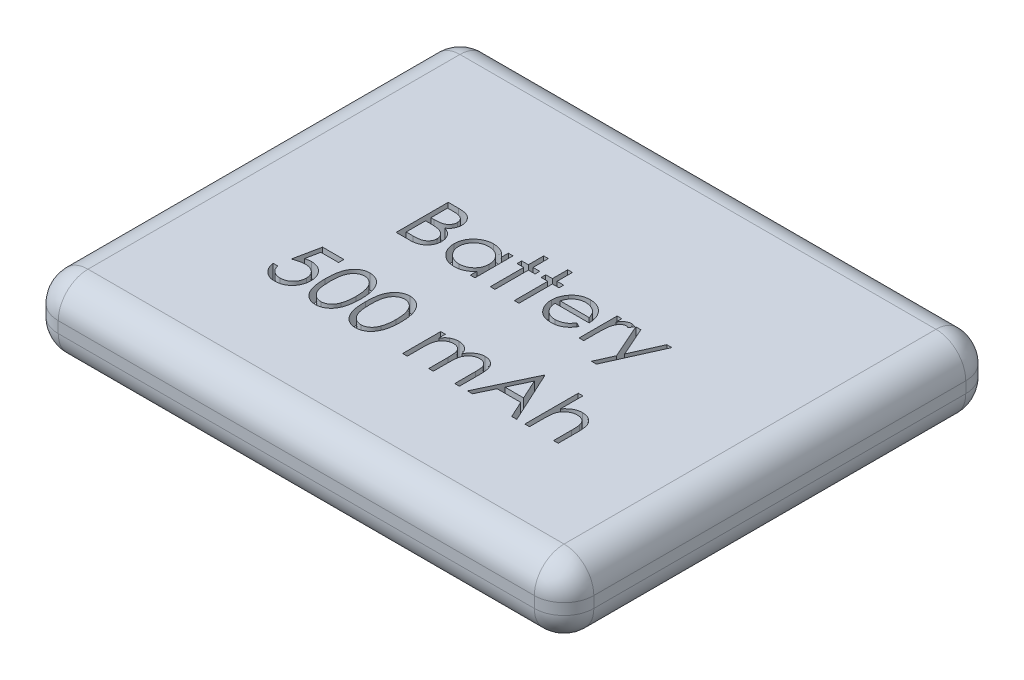
SolidWorks part; units mm, degrees
ref_plane "Front Plane" through (0, 0, 0) normal (0, 0, 1) x (1, 0, 0)
ref_plane "Top Plane" through (0, 0, 0) normal (0, 1, 0) x (1, 0, 0)
ref_plane "Right Plane" through (0, 0, 0) normal (1, 0, 0) x (0, 0, -1)
sketch "Sketch1" plane through (0, 0, 0) normal (0, 1, 0) x (1, 0, 0)
  line L1 (0, 0) -> (36, 0)
  line L2 (0, 0) -> (0, -29)
  line L3 (0, -29) -> (36, -29)
  line L4 (36, 0) -> (36, -29)
  dimension "D1" = 29
  dimension "D2" = 36
extrude "Boss-Extrude1" add sketch "Sketch1" along normal blind 4.75
fillet "Fillet1" radius 2 12 edges at (0, 0, 14.5) (18, 0, 0) (36, 0, 14.5) (18, 0, 29) (36, 4.75, 14.5) (18, 4.75, 0) (0, 4.75, 14.5) (18, 4.75, 29) (0, 2.375, 0) (0, 2.375, 29) (36, 2.375, 0) (36, 2.375, 29)
sketch "Sketch2" plane through (0, 4.75, 0) normal (0, 1, 0) x (1, 0, 0)
  line L0 (2, -14.5) -> (34, -14.5) construction
  line L1 (2, -2) -> (2, -27) construction
  line L2 (34, -27) -> (34, -2) construction
  text T0 "Battery\r\n500 mAh"
extrude "Cut-Extrude1" cut sketch "Sketch2" against normal blind 1
